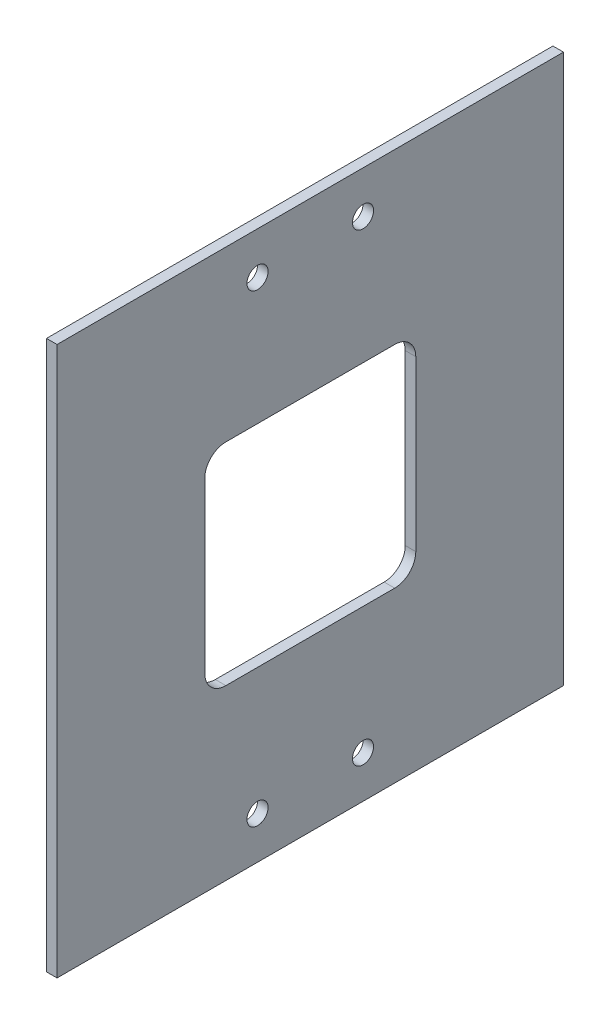
SolidWorks part; units mm, degrees
material "ASTM A36 Steel"
ref_plane "Front Plane" through (0, 0, 0) normal (0, 0, 1) x (1, 0, 0)
ref_plane "Top Plane" through (0, 0, 0) normal (0, 1, 0) x (1, 0, 0)
ref_plane "Right Plane" through (0, 0, 0) normal (1, 0, 0) x (0, 0, -1)
sketch "Sketch1" plane through (0, 0, 0) normal (1, 0, 0) x (0, 0, -1)
  line L0 (0, 2.6194) -> (0, -2.6194) construction
  line L1 (152.4, 82.55) -> (0, 82.55)
  line L2 (152.4, 82.55) -> (152.4, -82.55)
  line L3 (152.4, -82.55) -> (0, -82.55)
  line L4 (0, 82.55) -> (0, -82.55)
  line L5 (152.4, 82.55) -> (0, -82.55) construction
  line L6 (152.4, -82.55) -> (0, 82.55) construction
  line L7 (2.6194, 0) -> (-2.6194, 0) construction
  point P0 (76.2, 0)
  dimension "D1" = 152.4
  dimension "D2" = 165.1
extrude "Boss-Extrude1" add sketch "Sketch1" along normal blind 3.175
sketch "Sketch2" plane through (0, 0, 0) normal (-1, 0, 0) x (0, 0, 1)
  line L0 (-107.95, 25.4) -> (-107.95, -25.4)
  line L1 (-101.6, -31.75) -> (-50.8, -31.75)
  line L2 (-44.45, -25.4) -> (-44.45, 25.4)
  line L3 (-50.8, 31.75) -> (-101.6, 31.75)
  line L4 (-76.2, 31.75) -> (-76.2, -31.75) construction
  line L5 (0, 0) -> (-152.4, 0)
  line L6 (-152.4, -82.55) -> (-152.4, 82.55) construction
  arc A0 (-107.95, -25.4) -> (-101.6, -31.75) centre (-101.6, -25.4) ccw
  arc A1 (-50.8, -31.75) -> (-44.45, -25.4) centre (-50.8, -25.4) ccw
  arc A2 (-44.45, 25.4) -> (-50.8, 31.75) centre (-50.8, 25.4) ccw
  arc A3 (-101.6, 31.75) -> (-107.95, 25.4) centre (-101.6, 25.4) ccw
  point P19 (-76.2, 0)
  dimension "D1" = 6.35
  dimension "D2" = 63.5
  dimension "D3" = 63.5
extrude "Cut-Extrude1" cut sketch "Sketch2" against normal through all contours L4 L5 L0 A0 L1 | L4 L3 A3 L0 L5 | L3 L4 L5 L2 A2 | L5 L4 L1 A1 L2
sketch "Sketch3" plane through (0, 0, 0) normal (-1, 0, 0) x (0, 0, 1)
  line L0 (-76.2, 82.55) -> (-76.2, -82.55) construction
  line L1 (-152.4, 82.55) -> (0, 82.55) construction
  line L2 (0, -82.55) -> (-152.4, -82.55) construction
  line L3 (-92.075, -69.85) -> (-60.325, -69.85) construction
  line L4 (-92.075, 69.85) -> (-60.325, 69.85) construction
  circle A0 centre (-60.325, 69.85) radius 3.175
  circle A1 centre (-92.075, 69.85) radius 3.175
  circle A2 centre (-92.075, -69.85) radius 3.175
  circle A3 centre (-60.325, -69.85) radius 3.175
  point P10 (-76.2, 69.85)
  point P11 (-76.2, -69.85)
  dimension "D1" = 6.35
  dimension "D2" = 12.7
  dimension "D3" = 31.75
  dimension "D4" = 12.7
extrude "Cut-Extrude2" cut sketch "Sketch3" against normal through all
